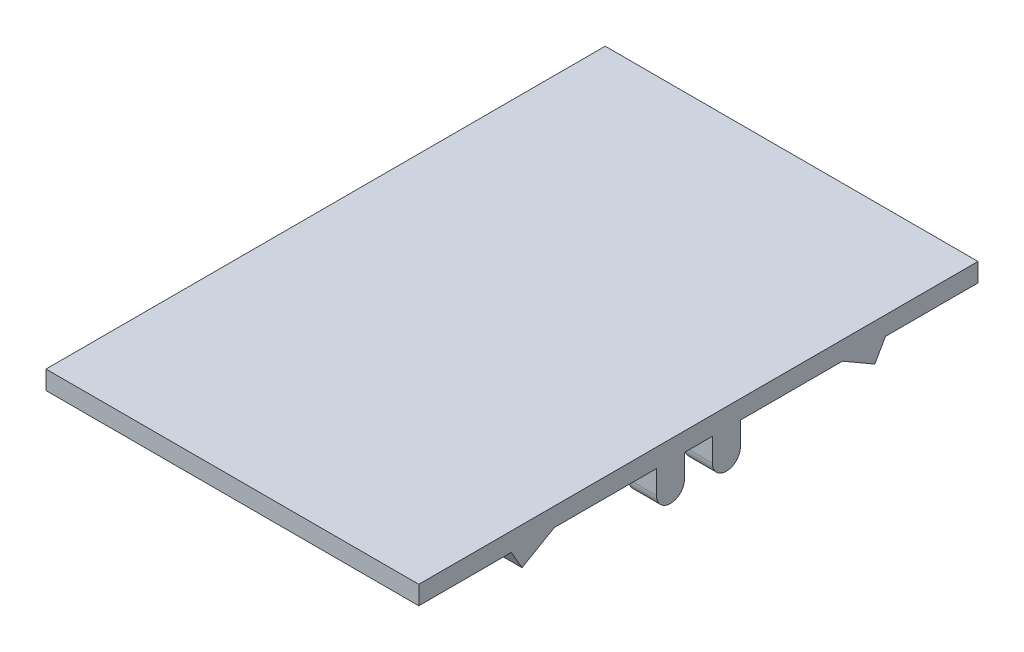
SolidWorks part; units mm, degrees
ref_plane "Front Plane" through (0, 0, 0) normal (0, 0, 1) x (1, 0, 0)
ref_plane "Top Plane" through (0, 0, 0) normal (0, 1, 0) x (1, 0, 0)
ref_plane "Right Plane" through (0, 0, 0) normal (1, 0, 0) x (0, 0, -1)
sketch "Sketch1" plane through (0, 0, 0) normal (0, 1, 0) x (1, 0, 0)
  line L1 (-200, -300) -> (200, -300)
  line L2 (-200, -300) -> (-200, 300)
  line L3 (-200, 300) -> (200, 300)
  line L4 (200, -300) -> (200, 300)
  line L5 (-200, -300) -> (200, 300) construction
  line L6 (-200, 300) -> (200, -300) construction
  point P0 (0, 0)
  dimension "D1" = 600
  dimension "D2" = 400
extrude "Boss-Extrude1" add sketch "Sketch1" along normal blind 20
sketch "Sketch3" plane through (200, 0, 0) normal (1, 0, 0) x (0, 0, -1)
  line L0 (-300, 0) -> (-30, 0) construction
  line L1 (-300, 0) -> (300, 0) construction
  line L2 (-30, 0) -> (-30, -25) construction
  line L3 (-45, -25) -> (-45, 0)
  line L4 (-45, 0) -> (-15, 0)
  line L5 (-15, 0) -> (-15, -25)
  arc A0 (-45, -25) -> (-15, -25) centre (-30, -25) ccw
  dimension "D2" = 25
  dimension "D3" = 15
  dimension "D1" = 270
extrude "Boss-Extrude2" add sketch "Sketch3" against normal blind 30
mirror "Mirror1" about plane through (0, 0, 0) normal (0, 0, 1) of "Boss-Extrude2"
mirror "Mirror2" about plane through (0, 0, 0) normal (1, 0, 0) of "Mirror1", "Boss-Extrude2"
sketch "Sketch4" plane through (200, 0, 0) normal (1, 0, 0) x (0, 0, -1)
  line L0 (-154.598, 0) -> (-189.239, -20)
  line L1 (-300, 0) -> (-45, 0) construction
  line L2 (-189.239, -20) -> (-200.7861, 0)
  line L3 (-200.7861, 0) -> (-154.598, 0)
  line L5 (-138.409, -86.2848) -> (-155.222, -61.4389) construction
  point P7 (-171.9185, -10)
  dimension "D1" = 30
  dimension "D2" = 15
  dimension "D3" = 40
extrude "Boss-Extrude3" add sketch "Sketch4" against normal blind 30
mirror "Mirror3" about plane through (0, 0, 0) normal (1, 0, 0) of "Boss-Extrude3"
mirror "Mirror4" about plane through (0, 0, 0) normal (0, 0, 1) of "Mirror3", "Boss-Extrude3"
